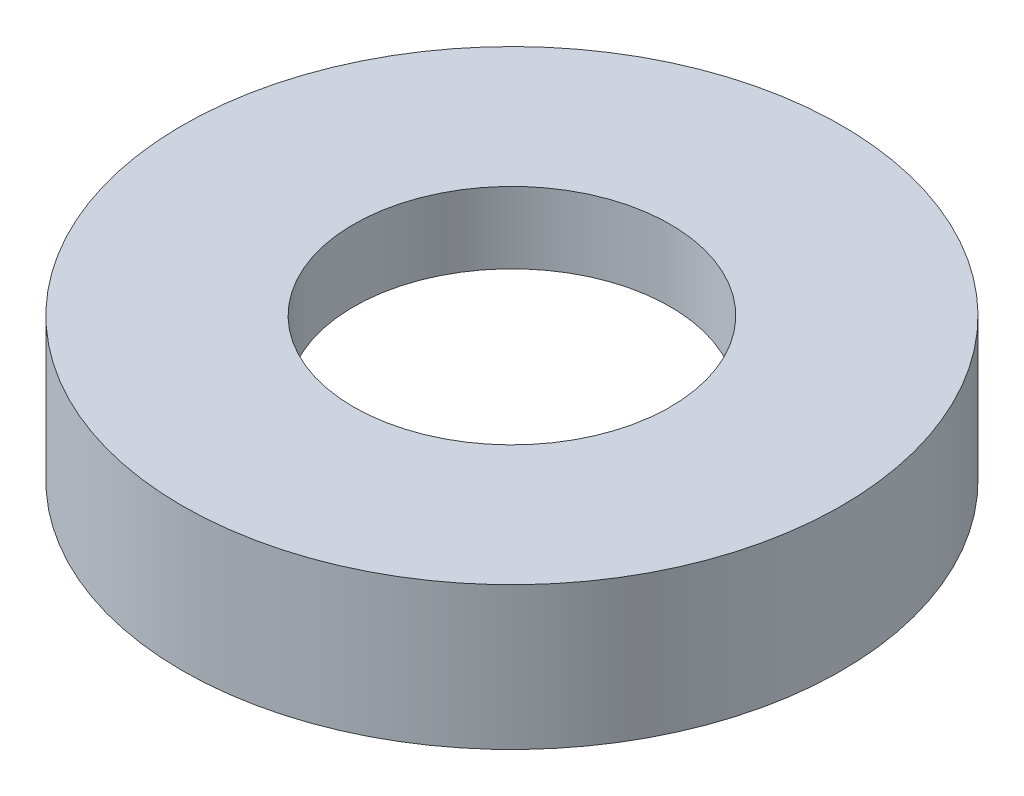
SolidWorks part; units mm, degrees
ref_plane "前视基准面" through (0, 0, 0) normal (0, 0, 1) x (1, 0, 0)
ref_plane "上视基准面" through (0, 0, 0) normal (0, 1, 0) x (1, 0, 0)
ref_plane "右视基准面" through (0, 0, 0) normal (1, 0, 0) x (0, 0, -1)
sketch "草图1" plane through (0, 0, 0) normal (0, 0, 1) x (1, 0, 0)
  line L0 (0, 60.0208) -> (0, -56.4315) construction
  line L1 (23.5, 0) -> (23.5, 4.5)
  line L2 (23.5, 4.5) -> (24.1, 4.5)
  line L3 (24.1, 4.5) -> (24.1, 5.5)
  line L4 (24.1, 5.5) -> (12.2, 5.5)
  line L5 (12.2, 5.5) -> (12.2, 11)
  line L6 (12.2, 11) -> (25.4, 11)
  line L7 (25.4, 11) -> (25.4, 0)
  line L8 (25.4, 0) -> (23.5, 0)
  point P5 (18.15, 5.5)
  dimension "D1" = 25.4
  dimension "D2" = 12.2
  dimension "D3" = 24.1
  dimension "D4" = 23.5
  dimension "D5" = 1
  dimension "D6" = 5.5
  dimension "D7" = 11
revolve "旋转1" add sketch "草图1" angle 360 about L0
cosmetic thread "装饰螺纹线1" parameters "D2"=25.4
cosmetic thread "装饰螺纹线2" parameters "D2"=48
